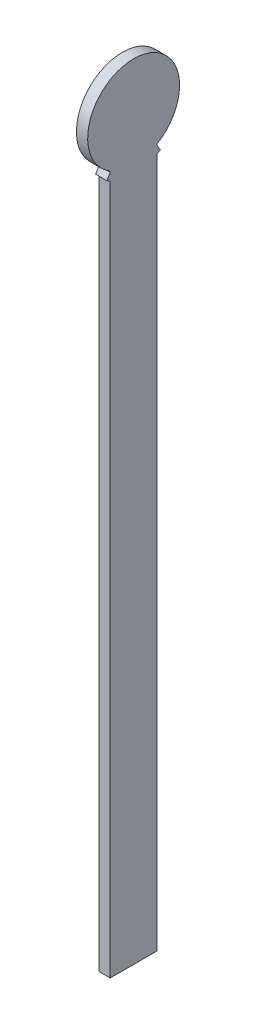
SolidWorks part; units mm, degrees
ref_plane "Front Plane" through (0, 0, 0) normal (0, 0, 1) x (1, 0, 0)
ref_plane "Top Plane" through (0, 0, 0) normal (0, 1, 0) x (1, 0, 0)
ref_plane "Right Plane" through (0, 0, 0) normal (1, 0, 0) x (0, 0, -1)
sketch "Sketch1" plane through (0, 0, 0) normal (1, 0, 0) x (0, 0, -1)
  line L0 (-12.5, 196.8) -> (12.5, 196.8)
  line L2 (-12.5, -196.8) -> (12.5, -196.8)
  line L3 (-12.5, -196.8) -> (-12.5, 166.8)
  line L5 (12.5, -196.8) -> (12.5, 166.8)
  line L7 (-12.5, 196.8) -> (-12.5, 166.8)
  line L8 (12.5, 196.8) -> (12.5, 166.8)
  line L9 (-12.5, 175.1494) -> (-14.25, 172.1183)
  line L10 (12.5, 175.1494) -> (14.25, 172.1183)
  arc A2 (-14.25, 172.1183) -> (14.25, 172.1183) centre (0, 196.8) ccw
  circle A3 centre (0, 196.8) radius 24.5
  point P0 (0, 0)
  point P4 (0, 0)
  point P15 (0, 196.8)
  dimension "D3" = 49
  dimension "D4" = 60
  dimension "D2" = 57
  dimension "D1" = 393.6
  dimension "D5" = 60
extrude "Boss-Extrude1" add sketch "Sketch1" along normal mid plane 6
